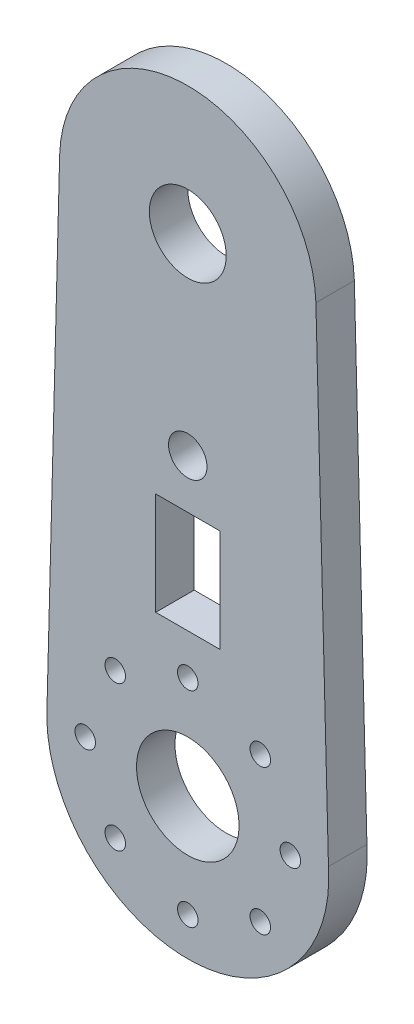
SolidWorks part; units mm, degrees
ref_plane "Ön Düzlem" through (0, 0, 0) normal (0, 0, 1) x (1, 0, 0)
ref_plane "Üst Düzlem" through (0, 0, 0) normal (0, 1, 0) x (1, 0, 0)
ref_plane "Sağ Düzlem" through (0, 0, 0) normal (1, 0, 0) x (0, 0, -1)
ref_plane "Düzlem1" through (0, 0, 3) normal (0, 0, 1) x (1, 0, 0)
sketch "Çizim1" plane through (0, 0, 3) normal (0, 0, 1) x (1, 0, 0)
  line L0 (10.9758, 0.7285) -> (9.9945, 38.3313)
  line L1 (-9.9945, 38.3313) -> (-10.9758, 0.7285)
  line L4 (-2.5, 11.1691) -> (2.5, 11.1691)
  line L5 (-2.5, 11.1691) -> (-2.5, 19.1691)
  line L6 (-2.5, 19.1691) -> (2.5, 19.1691)
  line L7 (2.5, 11.1691) -> (2.5, 19.1691)
  circle A1 centre (0, 8) radius 0.8
  circle A2 centre (5.6569, 5.6569) radius 0.8
  circle A3 centre (8, 0) radius 0.8
  circle A4 centre (5.6569, -5.6569) radius 0.8
  circle A5 centre (0, -8) radius 0.8
  circle A6 centre (-5.6569, -5.6569) radius 0.8
  circle A7 centre (-8, 0) radius 0.8
  circle A8 centre (0, 38) radius 3
  circle A9 centre (0, 0) radius 4
  circle A10 centre (0, 23) radius 1.5
  arc A11 (-10.9758, 0.7285) -> (10.9758, 0.7285) centre (0, 0) ccw
  arc A12 (9.9945, 38.3313) -> (-9.9945, 38.3313) centre (0, 38) ccw
  circle A13 centre (-5.6569, 5.6569) radius 0.8
  point P30 (0, 0)
  dimension "D1" = 6
  dimension "D2" = 5
  dimension "D3" = 1.6
  dimension "D6" = 8
  dimension "D4" = 8
extrude "Yükseklik-Ekstrüzyon1" add sketch "Çizim1" against normal blind 3
